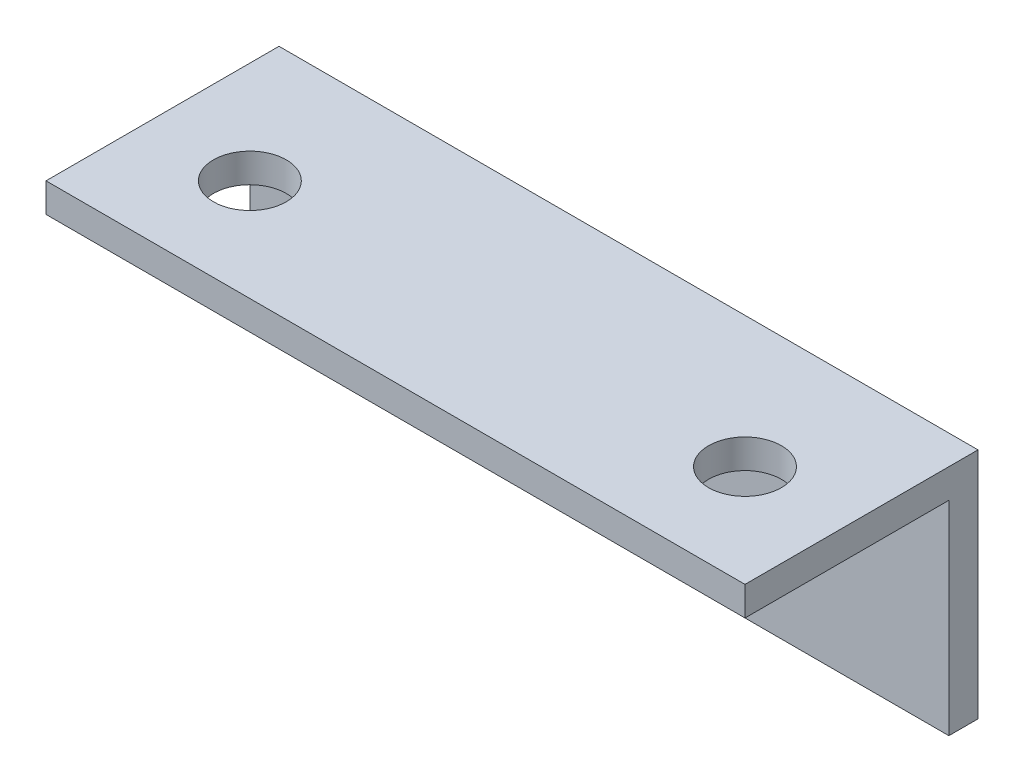
SolidWorks part; units mm, degrees
ref_plane "Front Plane" through (0, 0, 0) normal (0, 0, 1) x (1, 0, 0)
ref_plane "Top Plane" through (0, 0, 0) normal (0, 1, 0) x (1, 0, 0)
ref_plane "Right Plane" through (0, 0, 0) normal (1, 0, 0) x (0, 0, -1)
sketch "Sketch1" plane through (0, 0, 0) normal (1, 0, 0) x (0, 0, -1)
  line L0 (0, 0) -> (-25.4, 0)
  line L1 (0, 0) -> (0, -25.4)
  line L2 (0, -25.4) -> (-3.175, -25.4)
  line L3 (-3.175, -25.4) -> (-3.175, -3.175)
  line L4 (-3.175, -3.175) -> (-25.4, -3.175)
  line L5 (-25.4, -3.175) -> (-25.4, 0)
  dimension "D1" = 25.4
  dimension "D2" = 25.4
  dimension "D3" = 3.175
  dimension "D4" = 3.175
extrude "Boss-Extrude2" add sketch "Sketch1" along normal mid plane 76.2
hole_wizard "5/16 (0.3125) Diameter Hole1" positions "Sketch3" profile "Sketch2" hole size "5/16" standard "ANSI Inch" end condition up to next
sketch "Sketch3" plane through (0, 0, 0) normal (0, 1, 0) x (1, 0, 0)
  line L0 (-26.9875, -14.2875) -> (26.9875, -14.2875) construction
  line L1 (0, -14.2875) -> (0, 0) construction
  point P0 (-26.9875, -14.2875)
  point P2 (26.9875, -14.2875)
  dimension "D1" = 53.975
  dimension "D2" = 14.2875
sketch "Sketch2" plane through (-26.9875, 0, 14.2875) normal (1, 0, 0) x (0, 0, 1)
  line L0 (0, 0) -> (0, 3.175)
  line L1 (0, 3.175) -> (3.9688, 3.175)
  line L2 (3.9688, 3.175) -> (3.9687, 0)
  line L5 (3.9687, 0) -> (0, 0)
  line L11 (0, -6.35) -> (0, 107.95) construction
  dimension "Thru Hole Dia." = 7.9375
  dimension "Thru Hole Depth" = 3.175
sketch "Sketch4" plane through (0, 0, 0) normal (0, 0, -1) x (-1, 0, 0)
  line L0 (0, 0) -> (0, -25.4) construction
  line L1 (-38.1, 0) -> (38.1, 0) construction
  line L2 (-38.1, -25.4) -> (38.1, -25.4) construction
